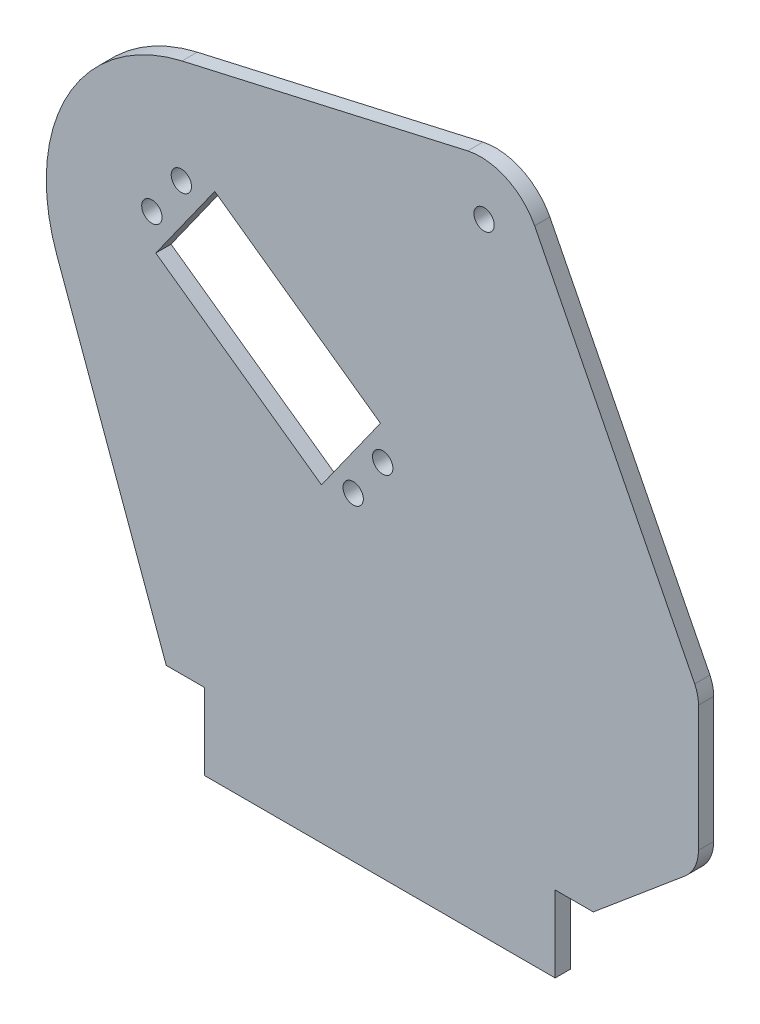
SolidWorks part; units mm, degrees
ref_plane "前基準面" through (0, 0, 0) normal (0, 0, 1) x (1, 0, 0)
ref_plane "上基準面" through (0, 0, 0) normal (0, 1, 0) x (1, 0, 0)
ref_plane "右基準面" through (0, 0, 0) normal (1, 0, 0) x (0, 0, -1)
sketch "草圖1" plane through (0, 0, 0) normal (0, 0, 1) x (1, 0, 0)
  line L0 (59.2978, 4.2188) -> (27.815, 66.5049)
  line L1 (14.6588, 72.6916) -> (-41.5351, 59.9099)
  line L2 (-66.1561, 14.5031) -> (-44.6452, -44.5974)
  line L3 (-44.6452, -44.5974) -> (-37.1452, -44.5974)
  line L4 (-37.1452, -44.5974) -> (-37.1452, -59.5974)
  line L5 (-37.1452, -59.5974) -> (31.8548, -59.5974)
  line L6 (31.8548, -59.5974) -> (31.8548, -44.5974)
  line L7 (31.8548, -44.5974) -> (39.3524, -44.5974)
  line L8 (39.3524, -44.5974) -> (57.4728, -29.3926)
  line L9 (60.038, -23.7449) -> (60.038, 0.97)
  line L14 (-40.9018, 32.7561) -> (-46.7004, 24.6089)
  line L17 (-46.7004, 24.6089) -> (-14.1117, 1.4145)
  line L18 (-14.1117, 1.4145) -> (-2.5145, 17.7088)
  line L19 (-2.5145, 17.7088) -> (-35.1031, 40.9032)
  line L20 (-35.1031, 40.9032) -> (-40.9018, 32.7561)
  circle A1 centre (17.8699, 62.6352) radius 2
  arc A2 (60.038, 0.97) -> (59.2978, 4.2188) centre (52.538, 0.97) ccw
  arc A3 (27.815, 66.5049) -> (14.6588, 72.6916) centre (17.1739, 60.9582) ccw
  arc A4 (-41.5351, 59.9099) -> (-66.1561, 14.5031) centre (-33.7367, 26.3028) ccw
  arc A5 (57.4728, -29.3926) -> (60.038, -23.7449) centre (52.538, -23.7449) ccw
  circle A7 centre (-2.0735, 11.2578) radius 2
  circle A8 centre (-7.8721, 3.1106) radius 2
  circle A9 centre (-41.6687, 39.439) radius 2
  circle A10 centre (-47.4673, 31.2919) radius 2
  point P31 (-44.568, 35.3655)
  dimension "D2" = 7.5
  dimension "D1" = 69
  dimension "D4" = 15
  dimension "D5" = 7.4977
  dimension "D6" = 15
  dimension "D7" = 140
  dimension "D8" = 70
  dimension "D10" = 10
extrude "填料-伸長1" add sketch "草圖1" along normal blind 3
